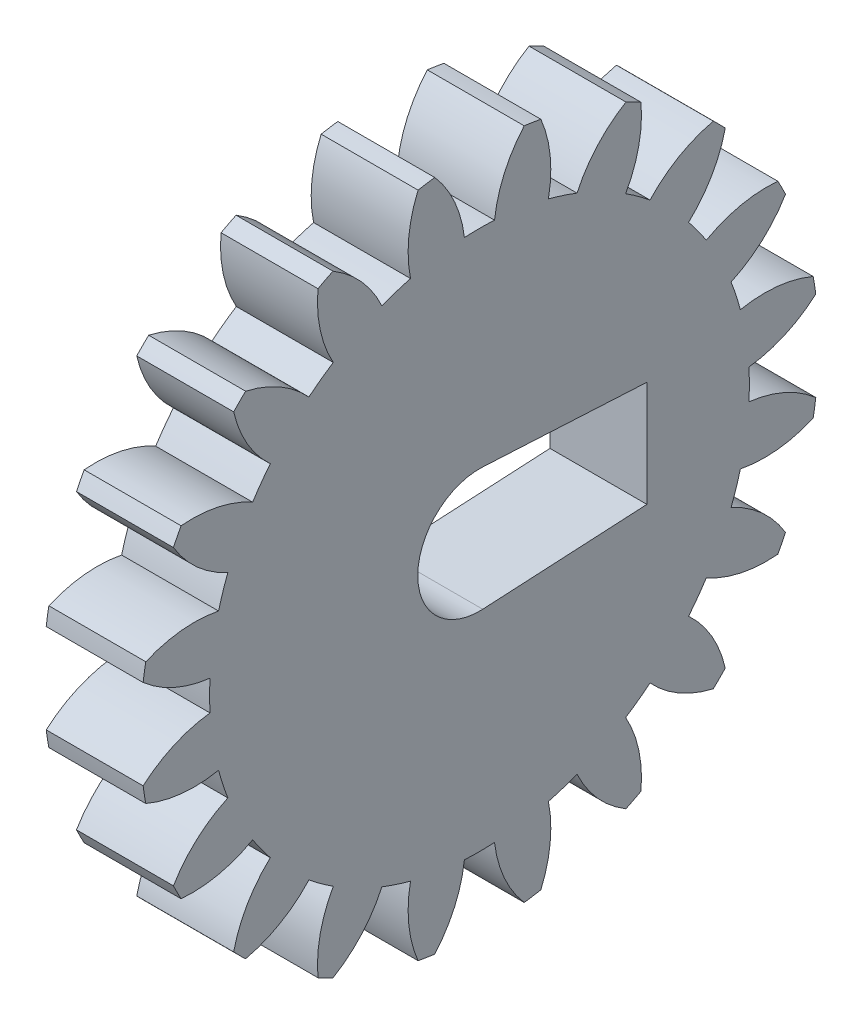
SolidWorks part; units mm, degrees
ref_plane "Plane1" through (0, 0, 0) normal (0, 0, 1) x (1, 0, 0)
ref_plane "Plane2" through (0, 0, 0) normal (0, 1, 0) x (1, 0, 0)
ref_plane "Plane3" through (0, 0, 0) normal (1, 0, 0) x (0, 0, -1)
other "Configuration Table"
sketch "HoldingSke" plane through (0, 0, 0) normal (0, 1, 0) x (1, 0, 0)
  line L0 (0, 0) -> (0.537, -0.1954)
  line L1 (-15, 0) -> (100, 0) construction
  line L2 (0, 0) -> (-2.1039, 2.3779)
  line L3 (0, 0) -> (-11.863, 4.5341)
  line L4 (0, 0) -> (8.1152, 2.9537)
  line L5 (0, 0) -> (-46.8476, -17.4728)
  line L6 (0, 0) -> (-8.2896, -5.593)
  line L7 (-2.1039, 2.3779) -> (8.6586, 51.2059)
  line L8 (-76.2, 54.61) -> (-76.1, 54.61)
  line L9 (-71.009, 38.7566) -> (-53.1078, 45.2721)
  line L10 (-76.2, 71.12) -> (104.1128, 71.12)
  line L11 (0, 0) -> (-10, 0)
  line L12 (-76.2, 101.6) -> (-76.147, 101.6)
  line L13 (24.9733, 27.94) -> (52.9518, 28.4284)
  line L14 (24.9733, 27.94) -> (24.9743, 27.94)
  line L15 (24.9733, 27.94) -> (100.4006, 29.5858)
  line L16 (-63.627, -1.75) -> (-12.827, -1.75)
  circle A0 centre (0, 0) radius 0.4
  circle A1 centre (0, 0) radius 15.3115
  circle A2 centre (0, 0) radius 37.5
  circle A3 centre (0, 0) radius 0.4
  dimension "MHD" = 30.623
  dimension "Hub_dia" = 75
  dimension "Bore" = 0.8
  dimension "MBD" = 0.8
  dimension "Num_teeth" = 20
  dimension "Pitch" = 0.5714
  dimension "Overall_len" = 50
  dimension "Show_teeth" = 20
  dimension "Thickness" = 10
  dimension "OAL" = 50.0001
  dimension "T_dim" = 0.1
  dimension "Ap" = 20
  dimension "H" = 19.05
  dimension "Pitch_radius" = 180.3128
  dimension "Width" = 10
  dimension "Backlash" = 0.053
  dimension "Addendum_fac" = 1
  dimension "Dedendum_fac" = 1.25
  dimension "Clearance_fac" = 0.25
  dimension "Dedendum_add" = 0.001
  dimension "Module" = 1.75
sketch "BasProSke" plane through (0, 0, 0) normal (0, 1, 0) x (1, 0, 0)
  line L0 (-10, 0) -> (60, 0) construction
  line L1 (0, 0) -> (0, 19.25)
  line L2 (0, 0) -> (10, 0)
  line L3 (10, 0) -> (10, 19.25)
  line L4 (10, 19.25) -> (0, 19.25)
  dimension "Thickness" = 10
  dimension "Diameter" = 38.5
revolve "Base-Revolve" add sketch "BasProSke" angle 360 about L0
sketch "TooCutSke" plane through (0, 0, 0) normal (1, 0, 0) x (0, 0, -1)
  line L1 (0, 0) -> (0, 107) construction
  line L2 (0, 0) -> (-1.4657, 17.4385) construction
  line L3 (0, 0) -> (-5.4605, 34.4765) construction
  line L4 (-1.4657, 17.4385) -> (-2.7303, 17.2382) construction
  arc A0 (0.8543, 15.2877) -> (-0.8543, 15.2877) centre (0, 0) ccw
  arc A1 (2.558, 19.1049) -> (-2.558, 19.1049) centre (0, 0) ccw
  circle A2 centre (0, 0) radius 17.5 construction
  circle A3 centre (0, 0) radius 16.4446 construction
  arc A4 (-0.8543, 15.2877) -> (-2.558, 19.1049) centre (-7.8067, 14.4734) ccw
  arc A5 (2.558, 19.1049) -> (0.8543, 15.2877) centre (7.8067, 14.4734) ccw
  dimension "Root_dia" = 30.623
  dimension "Overcut_dia" = 38.5508
  dimension "Pitch_dia" = 35
  dimension "Base_dia" = 32.8892
  dimension "Flank_rad" = 7
  dimension "Half_ang" = 9
  dimension "Half_CT" = 1.2803
extrude "ToothCut" cut sketch "TooCutSke" along normal through all
fillet "Breaks" [suppressed] radius 0.035
fillet "RootFillets" [suppressed] radius 0.4385
pattern_circular "TeethCuts" count 20 every 18 about axis through (-10, 0, 0) along (1, 0, 0) of "ToothCut", "RootFillets", "Breaks"
sketch "HubNeaOneSke" plane through (0, 0, 0) normal (-1, 0, 0) x (0, 0, 1)
  circle A0 centre (0, 0) radius 15.3115
  dimension "Diameter" = 30.623
extrude "HubNearOne" [suppressed] add sketch "HubNeaOneSke" along normal blind 40.0001
sketch "HubNeaBotSke" plane through (0, 0, 0) normal (-1, 0, 0) x (0, 0, 1)
  circle A0 centre (0, 0) radius 15.3115
  dimension "Diameter" = 30.623
extrude "HubNearBoth" [suppressed] add sketch "HubNeaBotSke" along normal blind 20
ref_plane "FarPln" through (10, 0, 0) normal (1, 0, 0) x (0, 0, -1)
sketch "HubFarSke" plane through (10, 0, 0) normal (1, 0, 0) x (0, 0, -1)
  circle A0 centre (0, 0) radius 15.3115
  dimension "Diameter" = 30.623
extrude "HubFar" [suppressed] add sketch "HubFarSke" along normal blind 20
sketch "BorSke" plane through (0, 0, 0) normal (1, 0, 0) x (0, 0, -1)
  circle A0 centre (0, 0) radius 0.4
  dimension "Diameter" = 0.8
extrude "Bore" cut sketch "BorSke" along normal mid plane 100.0001
sketch "KeySke" plane through (0, 0, 0) normal (1, 0, 0) x (0, 0, -1)
  line L0 (-0.05, 0) -> (-0.05, 0.5)
  line L1 (-0.05, 0.5) -> (0.05, 0.5)
  line L2 (0.05, 0.5) -> (0.05, 0)
  line L3 (0, 0) -> (0, 34) construction
  line L4 (-0.05, 0) -> (0.05, 0)
  dimension "Offset" = 0.5
  dimension "Width" = 0.1
extrude "Keyway" [suppressed] cut sketch "KeySke" along normal mid plane 100.0001
pattern_circular "Keyway2" [suppressed] count 2 every 90 about axis through (-10, 0, 0) along (1, 0, 0)
sketch "Sketch1" plane through (10, 0, 0) normal (1, 0, 0) x (0, 0, -1)
  circle A0 centre (0, 0) radius 2.5
  dimension "D1" = 5
extrude "Cut-Extrude1" cut sketch "Sketch1" against normal through all
sketch "草图1" plane through (0, 0, 0) normal (-1, 0, 0) x (0, 0, 1)
  line L1 (4, -4) -> (-4, -4)
  line L2 (4, -4) -> (4, 4)
  line L3 (4, 4) -> (-4, 4)
  line L4 (-4, -4) -> (-4, 4)
  line L5 (4, -4) -> (-4, 4) construction
  line L6 (4, 4) -> (-4, -4) construction
  point P0 (0, 0)
  dimension "D1" = 8
  dimension "D2" = 8
sketch "草图2" plane through (10, 0, 0) normal (1, 0, 0) x (0, 0, -1)
  line L0 (-3.5, 0) -> (9.5, 0) construction
  line L1 (9.5, 0) -> (9.5, 3)
  line L2 (9.5, 3) -> (9.5, 0)
  line L3 (9.5, -3) -> (9.5, 0)
  line L4 (9.5, 3) -> (0.1858, 3.4951)
  line L5 (9.5, -3) -> (0.1858, -3.4951)
  arc A1 (0.1858, 3.4951) -> (0.1858, -3.4951) centre (0, 0) ccw
  dimension "D1" = 7
  dimension "D3" = 3
  dimension "D2" = 13
  dimension "D4" = 3
extrude "切除-拉伸1" cut sketch "草图2" against normal blind 5.5 contours A1 L0 L1 L4 | L0 A1 L5 L3
sketch "草图4" plane through (0, 0, 0) normal (-1, 0, 0) x (0, 0, 1)
  circle A0 centre (0, 0) radius 25
  dimension "D1" = 50
extrude "切除-拉伸2" cut sketch "草图4" against normal blind 4.5
equation "' \"Module@HoldingSke\" = 6.35"
equation "' \"Num_teeth@HoldingSke\" = 12"
equation "' \"Ap@HoldingSke\" =  20"
equation "' \"Ap@HoldingSke\" = 20"
equation "' \"Width@HoldingSke\" = 0.5 * 25.4"
equation "' \"Hub_dia@HoldingSke\"= 1 * 25.4"
equation "' \"Hub_dia@HoldingSke\" = 1 * 25.4"
equation "' \"Overall_len@HoldingSke\" = 1.0 * 25.4"
equation "' \"Bore@HoldingSke\" = 0.75 * 25.4"
equation "' \"T_dim@HoldingSke\" = 0.1 * 25.4"
equation "' \"Width@KeySke\" = 0.25 * 25.4"
equation "' \"Show_teeth@HoldingSke\" = 13"
equation "' \"Backlash@HoldingSke\" = 0.009 * 25.4"
equation "' \"Addendum_fac@HoldingSke\" = 1.0"
equation "' \"Dedendum_fac@HoldingSke\" = 1.25"
equation "' \"Dedendum_add@HoldingSke\" = 0.00005 * 25.4"
equation "' \"Clearance_fac@HoldingSke\" = 0.25"
equation "\"Pitch@HoldingSke\" = 1 / \"Module@HoldingSke\""
equation "\"Overcut_dia@TooCutSke\" = (\"Num_teeth@HoldingSke\" + 2 * \"Addendum_fac@HoldingSke\") / \"Pitch@HoldingSke\" + 0.002 * 25.4"
equation "\"Pitch_dia@TooCutSke\" = \"Num_teeth@HoldingSke\" / \"Pitch@HoldingSke\""
equation "\"Base_dia@TooCutSke\" = \"Num_teeth@HoldingSke\" / \"Pitch@HoldingSke\" * cos((\"Ap@HoldingSke\"  * 3.14159265 / 180))"
equation "\"Root_dia@TooCutSke\" = (\"Num_teeth@HoldingSke\" + 2) / \"Pitch@HoldingSke\" - 2 * (\"Addendum_fac@HoldingSke\" + \"Dedendum_fac@HoldingSke\") / \"Pitch@HoldingSke\" - \"Dedendum_add@HoldingSke\" * 2"
equation "\"Half_ang@TooCutSke\" = 180 / \"Num_teeth@HoldingSke\""
equation "\"Half_CT@TooCutSke\" = \"Num_teeth@HoldingSke\" / \"Pitch@HoldingSke\" * sin((3.14159265 / 2 / \"Num_teeth@HoldingSke\")) / 2 - 7 * \"Backlash@HoldingSke\" / 4"
equation "\"Flank_rad@TooCutSke\" = \"Num_teeth@HoldingSke\" / \"Pitch@HoldingSke\" / 5"
equation "\"Radius@RootFillets\" = \"Clearance_fac@HoldingSke\" / \"Pitch@HoldingSke\" + \"Dedendum_add@HoldingSke\""
equation "\"Break_rad@Breaks\" = 0.02 / \"Pitch@HoldingSke\""
equation "\"Thickness@HoldingSke\" = \"Width@HoldingSke\""
equation "\"OAL@HoldingSke\" = \"Thickness@HoldingSke\""
equation "\"MHD@HoldingSke\" = (\"Num_teeth@HoldingSke\" + 2) / \"Pitch@HoldingSke\" - 2 * (\"Addendum_fac@HoldingSke\" + \"Dedendum_fac@HoldingSke\")  / \"Pitch@HoldingSke\" - \"Dedendum_add@HoldingSke\" * 2"
equation "\"MBD@HoldingSke\" = (\"Num_teeth@HoldingSke\" + 2) / \"Pitch@HoldingSke\" - 2 * (\"Addendum_fac@HoldingSke\" + \"Dedendum_fac@HoldingSke\")  / \"Pitch@HoldingSke\" - \"Dedendum_add@HoldingSke\" * 2 - 0.002 * 25.4"
equation "\"MHD@HoldingSke\" = ((sgn( \"MHD@HoldingSke\" - \"Hub_dia@HoldingSke\" )-1)*( \"MHD@HoldingSke\" - \"Hub_dia@HoldingSke\" ))/-2+ \"Hub_dia@HoldingSke\""
equation "\"MBD@HoldingSke\" = ((sgn( \"MBD@HoldingSke\" - \"Bore@HoldingSke\" )-1)*( \"MBD@HoldingSke\" - \"Bore@HoldingSke\" ))/-2+ \"Bore@HoldingSke\""
equation "\"OAL@HoldingSke\" = ((sgn( \"OAL@HoldingSke\" - \"Overall_len@HoldingSke\" )+1)*( \"OAL@HoldingSke\" - \"Overall_len@HoldingSke\" ))/2 + \"Overall_len@HoldingSke\" + 0.000002 * 25.4"
equation "\"Num_teeth@TeethCuts\" = int( \"Show_teeth@HoldingSke\" ) + 1"
equation "\"Num_teeth@TeethCuts\" = ((sgn( \"Num_teeth@TeethCuts\" - \"Num_teeth@HoldingSke\" )-1)*( \"Num_teeth@TeethCuts\" - \"Num_teeth@HoldingSke\" ))/-2+ \"Num_teeth@HoldingSke\""
equation "\"Num_teeth@TeethCuts\" = ((sgn( \"Num_teeth@TeethCuts\" - 2.0)+1)*( \"Num_teeth@TeethCuts\" - 2.0))/2 +2.0"
equation "\"Angle@TeethCuts\" = 360.0 / \"Num_teeth@HoldingSke\""
equation "\"Diameter@BasProSke\" = (\"Num_teeth@HoldingSke\" + 2 * \"Addendum_fac@HoldingSke\") / \"Pitch@HoldingSke\""
equation "\"Thickness@BasProSke\"  = \"Thickness@HoldingSke\""
equation "' \"Fillet_rad@BasProSke\" =  \"Thickness@HoldingSke\" * 0.05"
equation "' \"Fillet_rad@BasProSke\" = \"Thickness@HoldingSke\" * 0.05"
equation "\"MHD@HoldingSke\" = ((sgn( \"MHD@HoldingSke\" - \"Root_dia@TooCutSke\" )-1)*( \"MHD@HoldingSke\" - \"Root_dia@TooCutSke\" ))/-2+ \"Root_dia@TooCutSke\""
equation "\"Diameter@HubNeaOneSke\" = \"MHD@HoldingSke\""
equation "\"Length@HubNearOne\" = \"OAL@HoldingSke\" - \"Thickness@BasProSke\""
equation "\"Diameter@HubNeaBotSke\" = \"MHD@HoldingSke\""
equation "\"Length@HubNearBoth\" = ( \"OAL@HoldingSke\" - \"Thickness@BasProSke\" ) / 2.0"
equation "\"Thickness@FarPln\" = \"Thickness@BasProSke\""
equation "\"Diameter@HubFarSke\" = \"MHD@HoldingSke\""
equation "\"Length@HubFar\" = ( \"OAL@HoldingSke\" - \"Thickness@BasProSke\" ) / 2.0"
equation "\"Diameter@BorSke\" = \"MBD@HoldingSke\""
equation "\"D1@Bore\" = \"OAL@HoldingSke\" * 2.0"
equation "\"D1@Keyway\" = \"OAL@HoldingSke\" * 2.0"
equation "\"Offset@KeySke\" = \"T_dim@HoldingSke\" + \"MBD@HoldingSke\" / 2.0"
